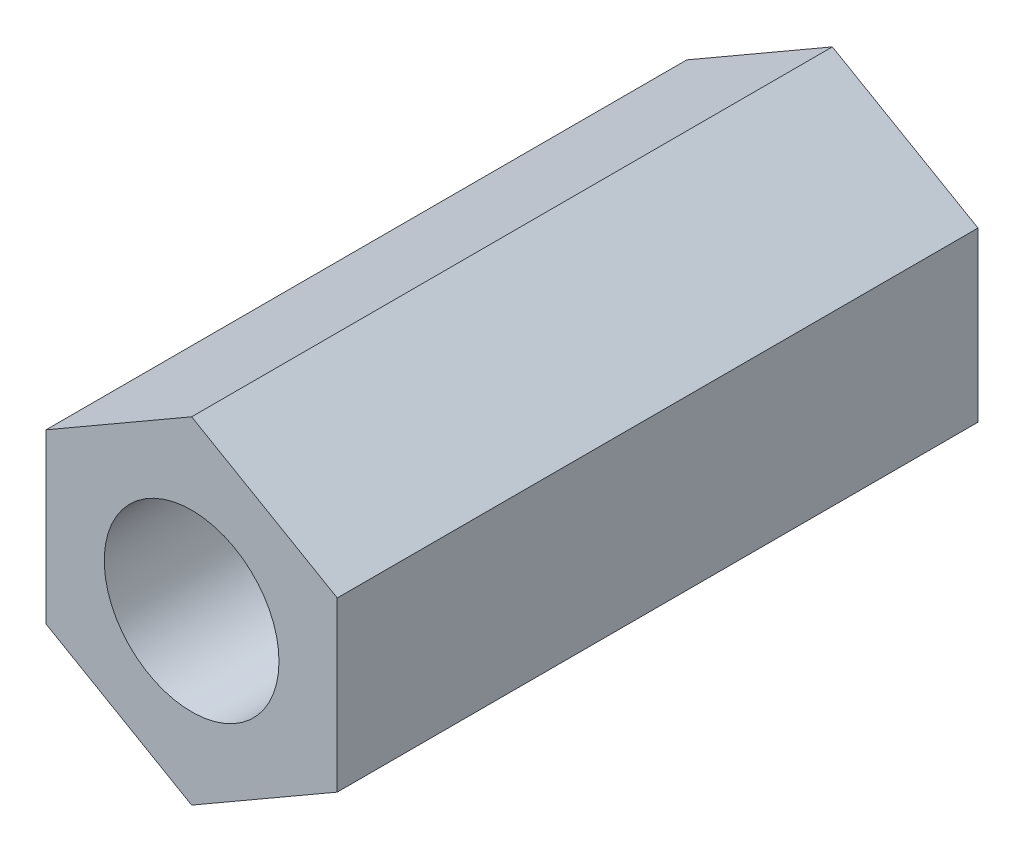
SolidWorks part; units mm, degrees
ref_plane "Plan de face" through (0, 0, 0) normal (0, 0, 1) x (1, 0, 0)
ref_plane "Plan de dessus" through (0, 0, 0) normal (0, 1, 0) x (1, 0, 0)
ref_plane "Plan de droite" through (0, 0, 0) normal (1, 0, 0) x (0, 0, -1)
sketch "Esquisse1" plane through (0, 0, 0) normal (0, 0, 1) x (1, 0, 0)
  line L1 (2.5, 1.4434) -> (0, 2.8868)
  line L2 (0, 2.8868) -> (-2.5, 1.4434)
  line L3 (-2.5, 1.4434) -> (-2.5, -1.4434)
  line L4 (-2.5, -1.4434) -> (0, -2.8868)
  line L5 (0, -2.8868) -> (2.5, -1.4434)
  line L6 (2.5, -1.4434) -> (2.5, 1.4434)
  circle A0 centre (0, 0) radius 2.5 construction
  circle A1 centre (0, 0) radius 1.5
  dimension "D2" = 3
  dimension "D1" = 5
extrude "Boss.-Extru.1" add sketch "Esquisse1" along normal blind 11
